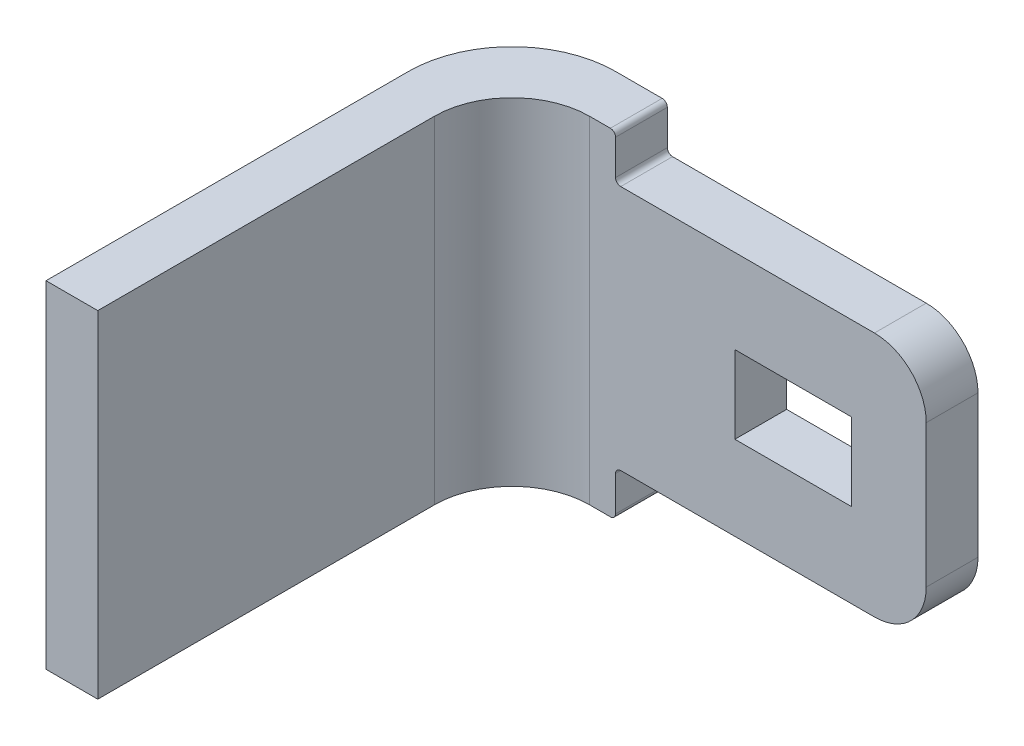
SolidWorks part; units mm, degrees
ref_plane "Спереди" through (0, 0, 0) normal (0, 0, 1) x (1, 0, 0)
ref_plane "Сверху" through (0, 0, 0) normal (0, 1, 0) x (1, 0, 0)
ref_plane "Справа" through (0, 0, 0) normal (1, 0, 0) x (0, 0, -1)
sketch "Эскиз1" plane through (0, 0, 0) normal (0, 1, 0) x (1, 0, 0)
  line L0 (-22.7025, 0) -> (-21.7025, 0)
  line L1 (-21.7025, 0) -> (-21.7025, 8)
  line L2 (-21.7025, 8) -> (-13.7025, 8)
  line L3 (-13.7025, 8) -> (-13.7025, 9)
  line L4 (-13.7025, 9) -> (-22.7025, 9)
  line L5 (-22.7025, 9) -> (-22.7025, 0)
  dimension "D1" = 1
  dimension "D2" = 1
  dimension "D3" = 9
  dimension "D4" = 9
extrude "Бобышка-Вытянуть1" add sketch "Эскиз1" along normal blind 6.5
fillet "Скругление1" radius 2 1 edges at (-22.7025, 3.25, -9)
fillet "Скругление2" radius 1.5 1 edges at (-21.7025, 3.25, -8)
sketch "Эскиз2" plane through (0, 0, -9) normal (0, 0, -1) x (-1, 0, 0)
  line L1 (13.7025, 0) -> (19.7025, 0)
  line L2 (13.7025, 0) -> (13.7025, 0.875)
  line L3 (13.7025, 0.875) -> (19.7025, 0.875)
  line L4 (19.7025, 0) -> (19.7025, 0.875)
  line L5 (13.7025, 6.5) -> (19.7025, 6.5)
  line L6 (13.7025, 6.5) -> (13.7025, 5.625)
  line L7 (13.7025, 5.625) -> (19.7025, 5.625)
  line L8 (19.7025, 6.5) -> (19.7025, 5.625)
  dimension "D1" = 0.875
  dimension "D2" = 6
extrude "Вырез-Вытянуть1" cut sketch "Эскиз2" against normal through all
fillet "Скругление4" radius 1 2 edges at (-13.7025, 5.625, -8.5) (-13.7025, 0.875, -8.5)
fillet "Скругление5" radius 0.1 2 edges at (-19.7025, 6.5, -8.5) (-19.7025, 0, -8.5)
fillet "Скругление6" radius 0.1 2 edges at (-19.7025, 0.875, -8.5) (-19.7025, 5.625, -8.5)
sketch "Эскиз3" plane through (0, 0, -9) normal (0, 0, -1) x (-1, 0, 0)
  line L1 (15.148, 2.5) -> (17.398, 2.5)
  line L2 (15.148, 2.5) -> (15.148, 4)
  line L3 (15.148, 4) -> (17.398, 4)
  line L4 (17.398, 2.5) -> (17.398, 4)
  line L8 (19.6025, 0.875) -> (14.7025, 0.875) construction
  dimension "D1" = 1.5
  dimension "D2" = 2.25
  dimension "D3" = 1.625
extrude "Вырез-Вытянуть2" cut sketch "Эскиз3" against normal through all
